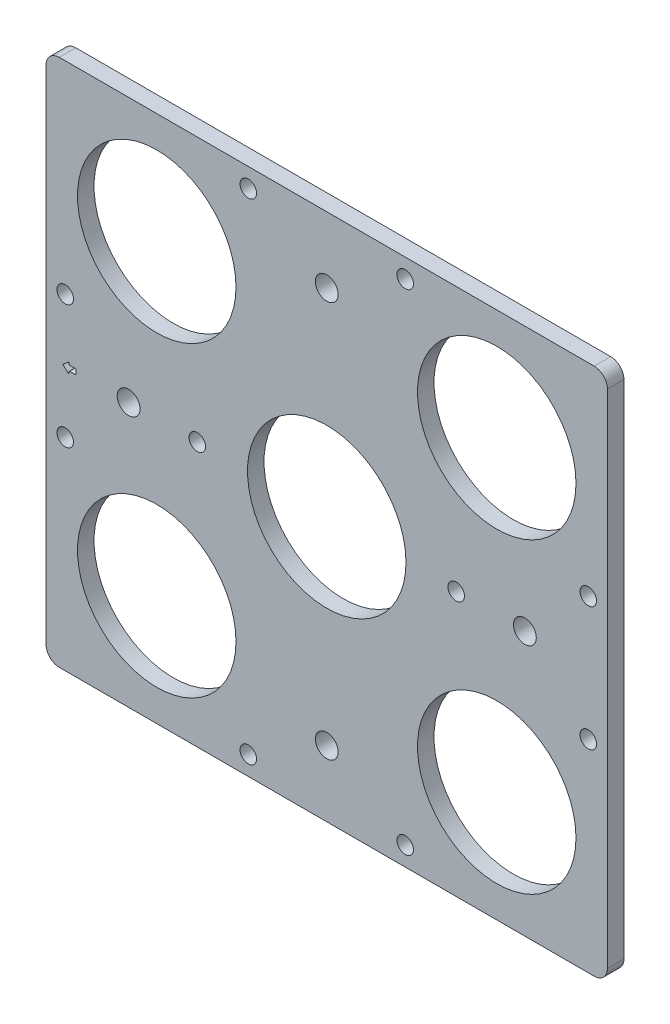
SolidWorks part; units mm, degrees
ref_plane "Front Plane" through (0, 0, 0) normal (0, 0, 1) x (1, 0, 0)
ref_plane "Top Plane" through (0, 0, 0) normal (0, 1, 0) x (1, 0, 0)
ref_plane "Right Plane" through (0, 0, 0) normal (1, 0, 0) x (0, 0, -1)
sketch "Sketch1" plane through (0, 0, 0) normal (0, 0, 1) x (1, 0, 0)
  line L1 (-70.0706, 113.3061) -> (37.8794, 113.3061)
  line L2 (-70.0706, 113.3061) -> (-70.0706, 11.7061)
  line L3 (-70.0706, 11.7061) -> (37.8794, 11.7061)
  line L4 (37.8794, 113.3061) -> (37.8794, 11.7061)
  line L5 (-70.0706, 113.3061) -> (37.8794, 11.7061) construction
  line L6 (-70.0706, 11.7061) -> (37.8794, 113.3061) construction
  point P0 (-16.0956, 62.5061)
  dimension "D1" = 101.6
  dimension "D2" = 107.95
extrude "Boss-Extrude1" add sketch "Sketch1" along normal blind 3.175
sketch "Sketch2" plane through (0, 0, 3.175) normal (0, 0, 1) x (1, 0, 0)
  line L0 (-70.0706, 113.3061) -> (37.8794, 11.7061) construction
  line L1 (37.8794, 113.3061) -> (-70.0706, 11.7061) construction
  circle A0 centre (-16.0956, 62.5061) radius 15.24
  circle A1 centre (16.5962, 32.9893) radius 15.24
  circle A2 centre (16.5962, 92.0229) radius 15.24
  circle A3 centre (-48.7874, 92.0229) radius 15.24
  circle A4 centre (-48.7874, 32.9893) radius 15.24
  dimension "D1" = 30.48
  dimension "D2" = 30.48
  dimension "D3" = 30.48
  dimension "D4" = 30.48
  dimension "D5" = 30.48
extrude "Cut-Extrude1" cut sketch "Sketch2" against normal up to next
sketch "Sketch3" plane through (0, 0, 3.175) normal (0, 0, 1) x (1, 0, 0)
  circle A0 centre (-31.1861, 109.6242) radius 1.5875
  circle A1 centre (-66.3887, 74.4216) radius 1.5875
  circle A2 centre (-1.0051, 109.6242) radius 1.5875
  circle A3 centre (34.1975, 74.4216) radius 1.5875
  circle A6 centre (-31.1861, 15.388) radius 1.5875
  circle A7 centre (-66.3887, 50.5906) radius 1.5875
  circle A8 centre (-1.0051, 15.388) radius 1.5875
  circle A9 centre (34.1975, 50.5906) radius 1.5875
  circle A10 centre (8.7964, 62.5061) radius 1.5875
  circle A11 centre (-40.9876, 62.5061) radius 1.5875
  dimension "D4" = 3.175
extrude "Cut-Extrude2" cut sketch "Sketch3" against normal up to next
sketch "Sketch4" plane through (0, 0, 3.175) normal (0, 0, 1) x (1, 0, 0)
  line L0 (-70.0706, 113.3061) -> (37.8794, 11.7061) construction
  line L2 (-54.1956, 24.4061) -> (22.0044, 24.4061) construction
  line L3 (-54.1956, 24.4061) -> (-54.1956, 100.6061) construction
  line L4 (-54.1956, 100.6061) -> (22.0044, 100.6061) construction
  line L5 (22.0044, 24.4061) -> (22.0044, 100.6061) construction
  line L6 (-54.1956, 24.4061) -> (22.0044, 100.6061) construction
  line L7 (-54.1956, 100.6061) -> (22.0044, 24.4061) construction
  circle A0 centre (-16.0956, 100.6061) radius 2.1971
  circle A1 centre (-16.0956, 24.4061) radius 2.1971
  circle A2 centre (-54.1956, 62.5061) radius 2.1971
  circle A3 centre (22.0044, 62.5061) radius 2.1971
  point P4 (-16.0956, 62.5061)
  dimension "D3" = 4.3942
  dimension "D1" = 76.2
  dimension "D2" = 76.2
extrude "Cut-Extrude3" cut sketch "Sketch4" against normal up to next
fillet "Fillet1" radius 2.54 4 edges at (37.8794, 11.7061, 1.5875) (-70.0706, 11.7061, 1.5875) (-70.0706, 113.3061, 1.5875) (37.8794, 113.3061, 1.5875)
sketch "Sketch5" plane through (0, 0, 3.175) normal (0, 0, 1) x (1, 0, 0)
  line L0 (-66.8956, 62.5061) -> (-64.3556, 62.5061) construction
  line L1 (-64.3556, 63.0141) -> (-64.3556, 61.9981)
  line L2 (-64.3556, 61.9981) -> (-65.6256, 61.9981)
  line L3 (-65.6256, 61.9981) -> (-65.6256, 61.4901)
  line L4 (-65.6256, 61.4901) -> (-66.8956, 62.5061)
  line L5 (-64.3556, 63.0141) -> (-65.6256, 63.0141)
  line L6 (-65.6256, 63.0141) -> (-65.6256, 63.5221)
  line L7 (-65.6256, 63.5221) -> (-66.8956, 62.5061)
  line L8 (35.3394, 113.3061) -> (-67.5306, 113.3061) construction
  line L9 (-16.0956, 102.8032) -> (-16.0956, 113.3061) construction
  line L10 (-56.3927, 62.5061) -> (-70.0706, 62.5061) construction
  line L11 (-70.0706, 110.7661) -> (-70.0706, 14.2461) construction
  circle A0 centre (-16.0956, 100.6061) radius 2.1971 construction
  circle A1 centre (-54.1956, 62.5061) radius 2.1971 construction
  dimension "D1" = 1.27
  dimension "D2" = 1.27
  dimension "D3" = 0.508
  dimension "D4" = 1.016
  dimension "D5" = 3.175
extrude "Cut-Extrude4" cut sketch "Sketch5" against normal through all contours L4 L7 L6 L5 L1 L2 L3
fillet "Fillet3" radius 0.0635 7 edges at (-66.8956, 62.5061, 1.5875) (-65.6256, 63.5221, 1.5875) (-64.3556, 63.0141, 1.5875) (-64.3556, 61.9981, 1.5875) (-65.6256, 63.0141, 1.5875) (-65.6256, 61.4901, 1.5875) (-65.6256, 61.9981, 1.5875)
